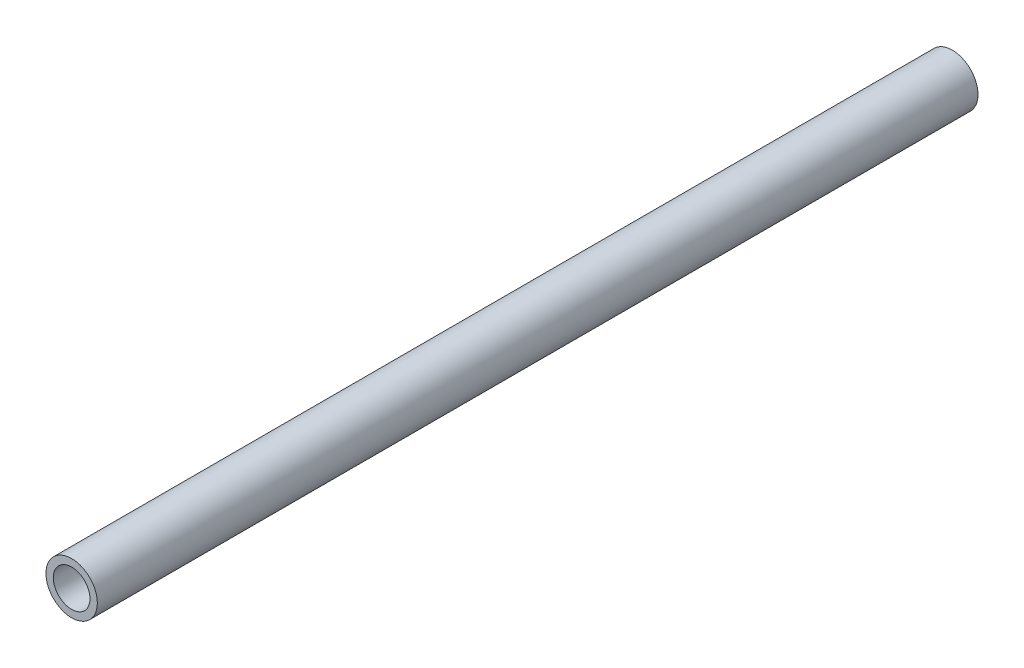
SolidWorks part; units mm, degrees
ref_plane "Front Plane" through (0, 0, 0) normal (0, 0, 1) x (1, 0, 0)
ref_plane "Top Plane" through (0, 0, 0) normal (0, 1, 0) x (1, 0, 0)
ref_plane "Right Plane" through (0, 0, 0) normal (1, 0, 0) x (0, 0, -1)
sketch "Sketch1" plane through (0, 0, 0) normal (0, 0, 1) x (1, 0, 0)
  circle A0 centre (0, 0) radius 9.525
  circle A1 centre (0, 0) radius 13.335
  dimension "D1" = 26.67
  dimension "D2" = 19.05
extrude "Boss-Extrude1" add sketch "Sketch1" along normal blind 457.2
